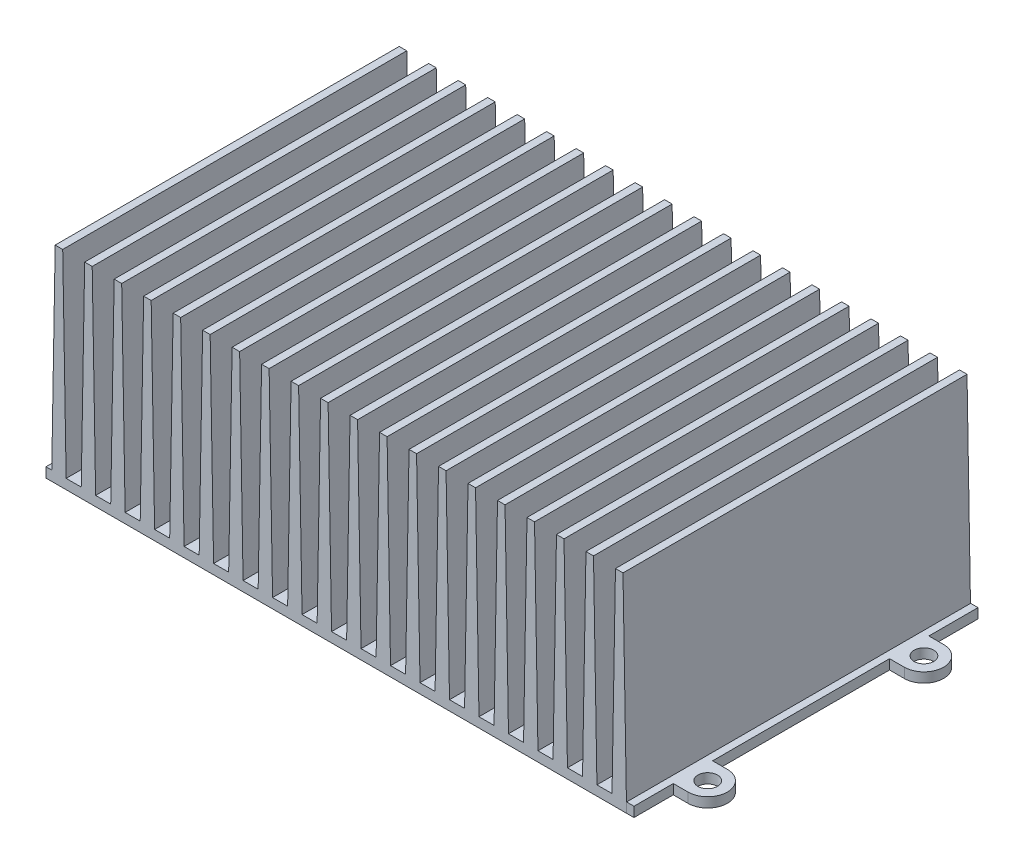
SolidWorks part; units mm, degrees
ref_plane "Front Plane" through (0, 0, 0) normal (0, 0, 1) x (1, 0, 0)
ref_plane "Top Plane" through (0, 0, 0) normal (0, 1, 0) x (1, 0, 0)
ref_plane "Right Plane" through (0, 0, 0) normal (1, 0, 0) x (0, 0, -1)
sketch "Sketch1" plane through (0, 0, 0) normal (0, 0, 1) x (1, 0, 0)
  line L0 (-163.5735, 50.8) -> (-67.4277, 50.8)
  line L1 (0, 0) -> (-228.6, 0)
  line L2 (0, 0) -> (0, 1066.8)
  line L3 (0, 1066.8) -> (-228.6, 1066.8)
  line L4 (-228.6, 0) -> (-228.6, 1066.8)
  line L5 (-228.6, 0) -> (-152.4, 0)
  line L6 (0, 0) -> (-76.2, 0)
  line L7 (-228.6, 0) -> (-209.9789, 1066.8)
  line L8 (-152.4, 50.8) -> (-152.4, 1066.8)
  line L9 (-153.2867, 50.8) -> (-171.0211, 1066.8)
  line L10 (-76.2, 50.8) -> (-76.2, 1066.8)
  line L11 (-75.3133, 50.8) -> (-57.5789, 1066.8)
  line L12 (0, 0) -> (-18.6211, 1066.8)
  point P4 (0, 0)
  dimension "D1" = 1066.8
  dimension "D2" = 228.6
  dimension "D3" = 50.8
  dimension "D4" = 76.2
  dimension "D5" = 76.2
  dimension "D6" = 1
  dimension "D7" = 1
  dimension "D8" = 1
  dimension "D9" = 1
extrude "Boss-Extrude2" add sketch "Sketch1" along normal blind 1778
pattern_linear "LPattern3" count 19 spacing 152.4 along (-1, 0, 0) of "Boss-Extrude2"
sketch "Sketch3" plane through (0, 0, 0) normal (0, 1, 0) x (1, 0, 0)
  line L0 (-2971.8, -1778) -> (-2953.1789, -1778) construction
  line L1 (0, -1778) -> (38.1, -1778)
  line L2 (0, -1778) -> (0, 0)
  line L3 (0, 0) -> (38.1, 0)
  line L4 (38.1, -1778) -> (38.1, 0)
  line L5 (-2962.4895, -1778) -> (-3000.5895, -1778)
  line L6 (-2962.4895, -1778) -> (-2962.4895, 0)
  line L7 (-2962.4895, 0) -> (-3000.5895, 0)
  line L8 (-3000.5895, -1778) -> (-3000.5895, 0)
  dimension "D1" = 38.1
  dimension "D2" = 38.1
extrude "Boss-Extrude3" add sketch "Sketch3" along normal blind 50.8
sketch "Sketch4" plane through (0, 50.8, 0) normal (0, 1, 0) x (1, 0, 0)
  line L0 (38.1, -1778) -> (38.1, -1473.2)
  line L1 (38.1, -1778) -> (38.1, 0) construction
  line L2 (38.1, -1473.2) -> (114.3, -1473.2)
  line L3 (38.1, -1574.8) -> (114.3, -1574.8)
  line L4 (38.1, -1371.6) -> (114.3, -1371.6)
  circle A0 centre (114.3, -1473.2) radius 50.8
  arc A1 (114.3, -1371.6) -> (114.3, -1574.8) centre (114.3, -1473.2) cw
  dimension "D3" = 101.6
  dimension "D1" = 304.8
  dimension "D2" = 76.2
  dimension "D4" = 101.6
  dimension "D5" = 101.6
  dimension "D6" = 76.2
  dimension "D7" = 76.2
extrude "Boss-Extrude5" add sketch "Sketch4" against normal blind 50.8
pattern_linear "LPattern4" count 2 spacing 1117.6 along (0, 0, -1) of "Boss-Extrude5"
sketch "Sketch5" plane through (0, 50.8, 0) normal (0, 1, 0) x (1, 0, 0)
  line L0 (-3000.5895, -1778) -> (-3000.5895, -1473.2)
  line L1 (-3000.5895, 0) -> (-3000.5895, -1778) construction
  line L2 (-3000.5895, -1473.2) -> (-3076.7895, -1473.2)
  line L3 (-3000.5895, -1574.8) -> (-3076.7895, -1574.8)
  line L4 (-3000.5895, -1371.6) -> (-3076.7895, -1371.6)
  circle A0 centre (-3076.7895, -1473.2) radius 50.8
  arc A1 (-3076.7895, -1574.8) -> (-3076.7895, -1371.6) centre (-3076.7895, -1473.2) cw
  dimension "D3" = 101.6
  dimension "D1" = 304.8
  dimension "D2" = 76.2
  dimension "D4" = 101.6
  dimension "D5" = 101.6
extrude "Boss-Extrude6" add sketch "Sketch5" against normal blind 50.8
pattern_linear "LPattern5" count 2 spacing 1117.6 along (0, 0, -1) of "Boss-Extrude6"
